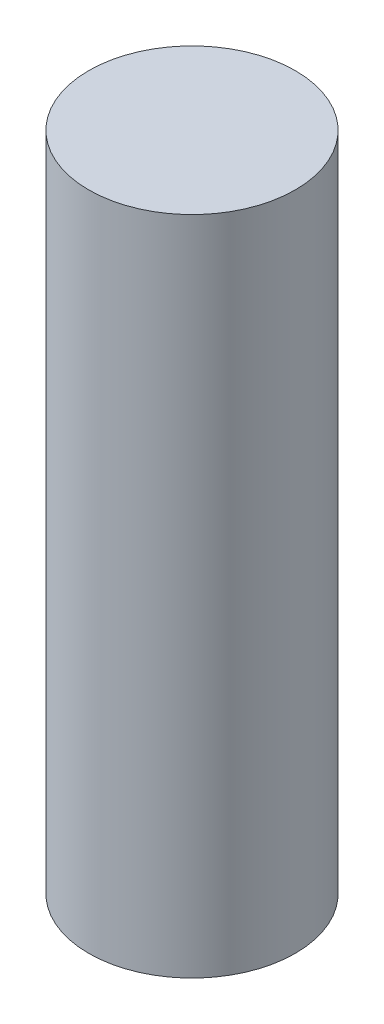
SolidWorks part; units mm, degrees
ref_plane "Front Plane" through (0, 0, 0) normal (0, 0, 1) x (1, 0, 0)
ref_plane "Top Plane" through (0, 0, 0) normal (0, 1, 0) x (1, 0, 0)
ref_plane "Right Plane" through (0, 0, 0) normal (1, 0, 0) x (0, 0, -1)
sketch "Sketch1" plane through (0, 0, 0) normal (0, 1, 0) x (1, 0, 0)
  circle A0 centre (0, 0) radius 5
  dimension "D1" = 10
extrude "Boss-Extrude1" add sketch "Sketch1" along normal blind 32
